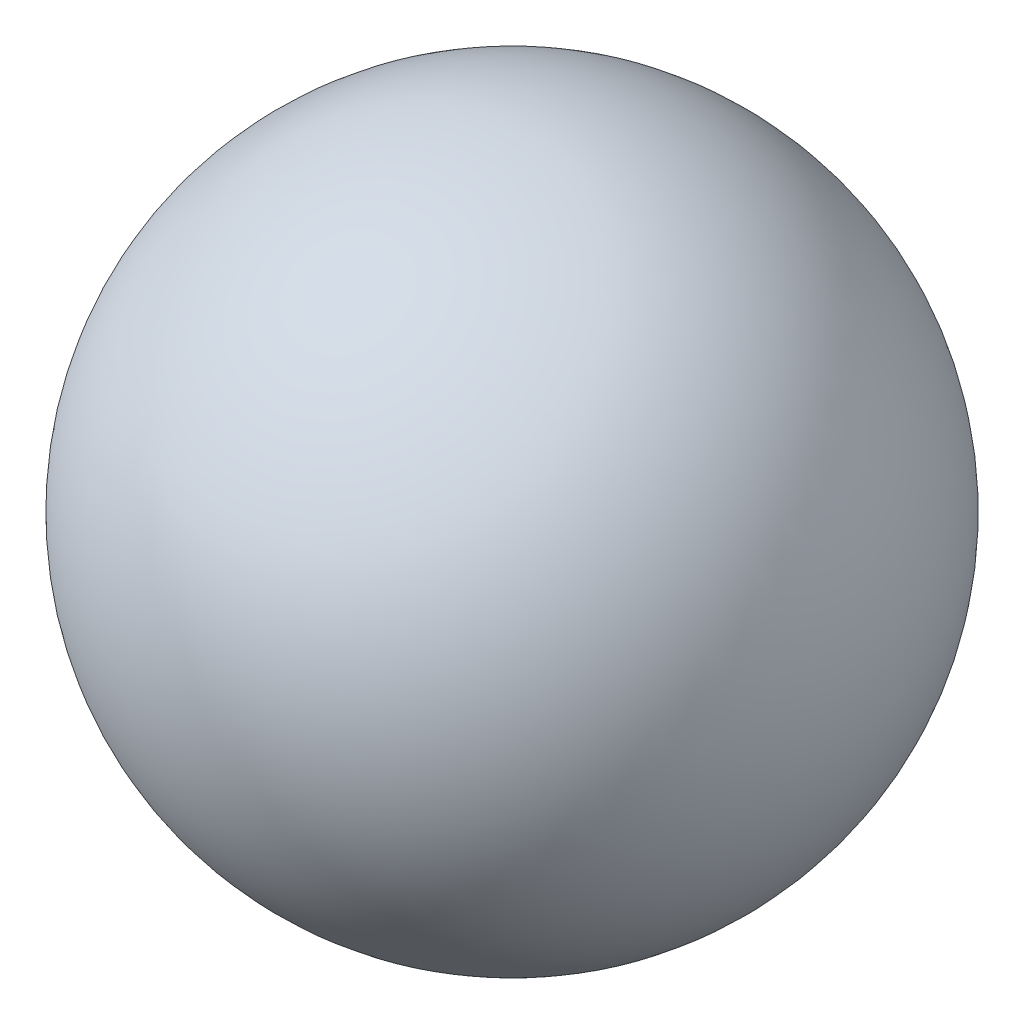
SolidWorks part; units mm, degrees
ref_plane "Plan de face" through (0, 0, 0) normal (0, 0, 1) x (1, 0, 0)
ref_plane "Plan de dessus" through (0, 0, 0) normal (0, 1, 0) x (1, 0, 0)
ref_plane "Plan de droite" through (0, 0, 0) normal (1, 0, 0) x (0, 0, -1)
sketch "Esquisse1" plane through (0, 0, 0) normal (0, 0, 1) x (1, 0, 0)
  line L0 (0, 2.5) -> (0, -2.5)
  arc A0 (0, 2.5) -> (0, -2.5) centre (0, 0) ccw
  dimension "D1" = 5
revolve "Révolution2" add sketch "Esquisse1" angle 360 about L0
sketch "Esquisse2" plane through (0, 0, 0) normal (0, 0, 1) x (1, 0, 0)
  point P0 (0, 0)
